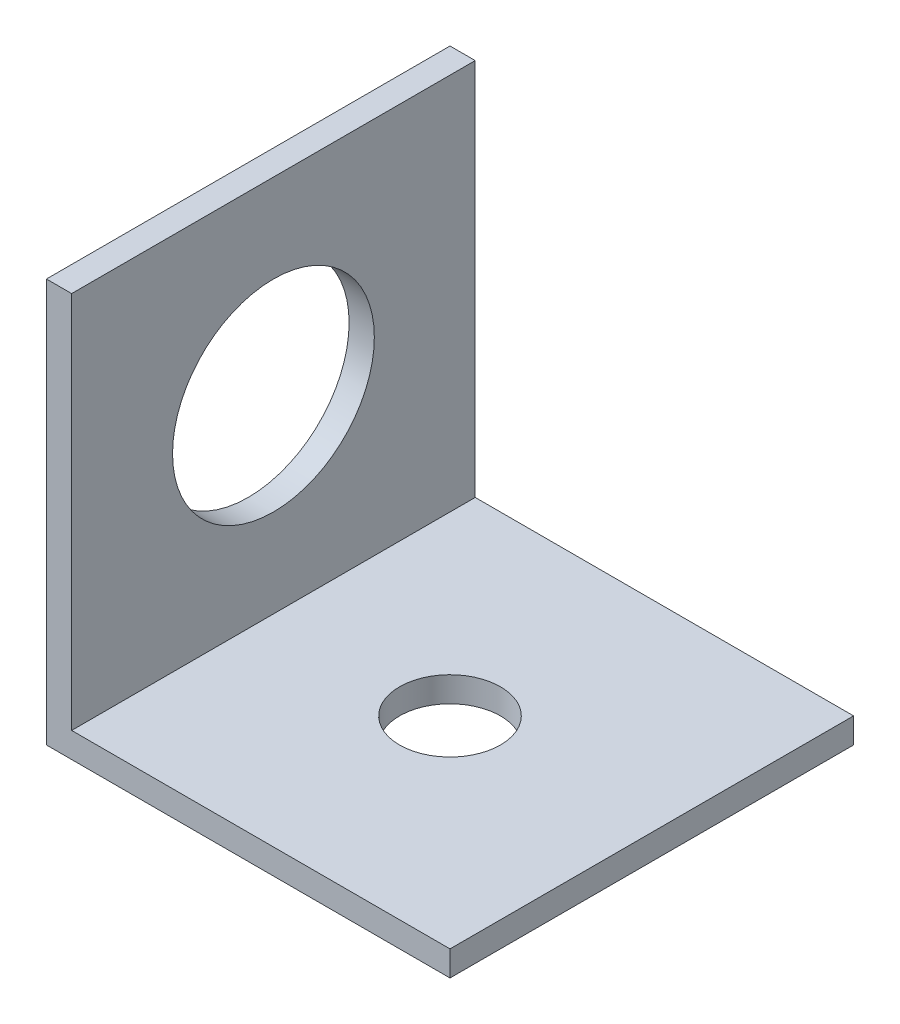
SolidWorks part; units mm, degrees
ref_plane "Front Plane" through (0, 0, 0) normal (0, 0, 1) x (1, 0, 0)
ref_plane "Top Plane" through (0, 0, 0) normal (0, 1, 0) x (1, 0, 0)
ref_plane "Right Plane" through (0, 0, 0) normal (1, 0, 0) x (0, 0, -1)
sketch "Sketch1" plane through (0, 0, 0) normal (0, 0, 1) x (1, 0, 0)
  line L0 (0, 0) -> (0, 25.4)
  line L1 (0, 25.4) -> (1.5875, 25.4)
  line L2 (1.5875, 25.4) -> (1.5875, 1.5875)
  line L3 (1.5875, 1.5875) -> (25.4, 1.5875)
  line L4 (25.4, 1.5875) -> (25.4, 0)
  line L5 (25.4, 0) -> (0, 0)
  dimension "D1" = 25.4
  dimension "D2" = 25.4
  dimension "D3" = 1.5875
  dimension "D4" = 1.5875
  dimension "D5" = 23.8125
extrude "Boss-Extrude1" add sketch "Sketch1" along normal blind 25.4
sketch "Sketch2" plane through (0, 1.5875, 0) normal (0, 1, 0) x (1, 0, 0)
  line L0 (0, -25.4) -> (25.4, 0) construction
  line L1 (0, -25.4) -> (0, 0) construction
  circle A0 centre (12.7, -12.7) radius 3.175
  dimension "D1" = 6.35
extrude "Cut-Extrude1" cut sketch "Sketch2" against normal blind 25.4
sketch "Sketch3" plane through (1.5875, 0, 0) normal (1, 0, 0) x (0, 0, -1)
  line L0 (-25.4, 1.5875) -> (0, 25.4) construction
  circle A0 centre (-12.7, 13.4938) radius 6.35
  dimension "D1" = 12.7
extrude "Cut-Extrude2" cut sketch "Sketch3" against normal blind 25.4
